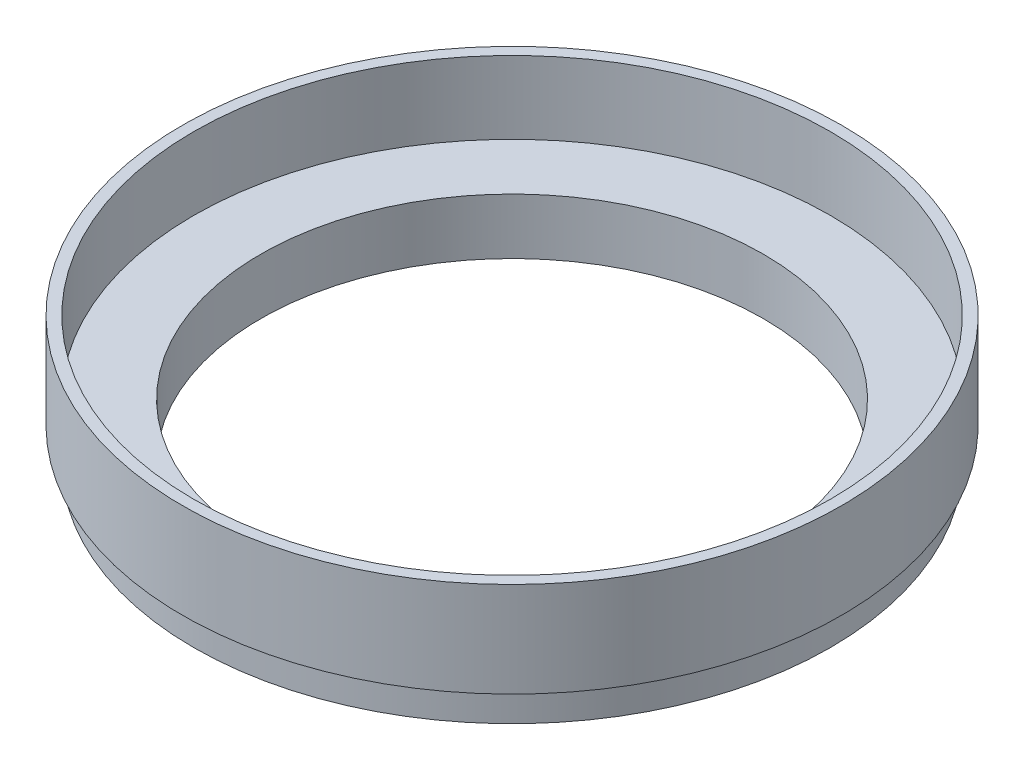
SolidWorks part; units mm, degrees
ref_plane "Piano frontale" through (0, 0, 0) normal (0, 0, 1) x (1, 0, 0)
ref_plane "Piano superiore" through (0, 0, 0) normal (0, 1, 0) x (1, 0, 0)
ref_plane "Piano destro" through (0, 0, 0) normal (1, 0, 0) x (0, 0, -1)
sketch "Schizzo1" plane through (0, 0, 0) normal (0, 0, 1) x (1, 0, 0)
  line L1 (28.5, 0) -> (28.5, 3)
  line L2 (28.5, 3) -> (29.5, 3)
  line L3 (29.5, 3) -> (29.5, 11.5)
  line L5 (28.5, 11.5) -> (28.5, 5)
  line L6 (28.5, 5) -> (22.5, 5)
  line L7 (22.5, 5) -> (22.5, 0)
  line L8 (22.5, 0) -> (24.5, 0)
  line L9 (24.5, 0) -> (24.5, 2)
  line L10 (24.5, 2) -> (26.5, 2)
  line L11 (26.5, 2) -> (26.5, 0)
  line L12 (26.5, 0) -> (28.5, 0)
  line L13 (28.5, 11.5) -> (29.5, 11.5)
  line L14 (0, 0) -> (0, 5) construction
  dimension "D1" = 22.5
  dimension "D2" = 2
  dimension "D3" = 2
  dimension "D4" = 3
  dimension "D5" = 1
  dimension "D6" = 8.5
  dimension "D7" = 5
  dimension "D8" = 6
  dimension "D9" = 6.5
  dimension "D10" = 1
revolve "Rivoluzione1" add sketch "Schizzo1" angle 360 about L14
